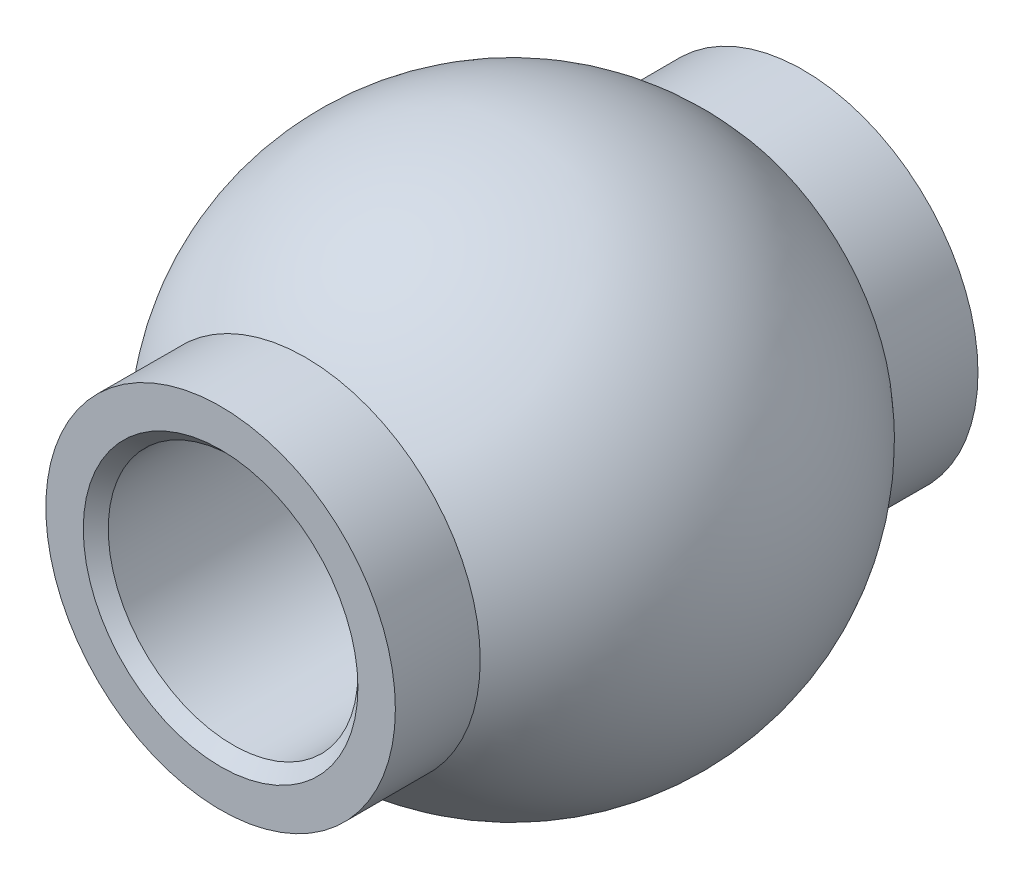
SolidWorks part; units mm, degrees
ref_plane "Front" through (0, 0, 0) normal (0, 0, 1) x (1, 0, 0)
ref_plane "Top" through (0, 0, 0) normal (0, 1, 0) x (1, 0, 0)
ref_plane "Right" through (0, 0, 0) normal (1, 0, 0) x (0, 0, -1)
sketch "Sketch1" plane through (0, 0, 0) normal (0, 0, 1) x (1, 0, 0)
  line L0 (0, 0) -> (0, -34.925)
  line L1 (0, -34.925) -> (4.7625, -34.925)
  line L2 (4.7625, -34.925) -> (4.7625, 0)
  line L3 (4.7625, 0) -> (0, 0)
  line L5 (0, 33.3375) -> (0, 0) construction
  line L6 (0, 33.3375) -> (14.2875, 33.3375) construction
  line L7 (14.2875, 33.3375) -> (14.2875, 19.05) construction
  line L8 (-4.7625, -34.925) -> (-4.7625, 0) construction
  line L9 (3.8092, -34.925) -> (4.7625, -33.9717)
  line L10 (4.8772, -34.8588) -> (4.8772, -35.918) construction
  line L11 (4.8772, -35.918) -> (3.9599, -35.3884) construction
  line L12 (3.9599, -35.3884) -> (4.8772, -34.8588) construction
  line L13 (3.9599, -35.3884) -> (4.0745, -35.3884) construction
  line L14 (4.8772, -35.3884) -> (4.7625, -35.3884) construction
  line L15 (4.0745, -35.4546) -> (4.0745, -35.3222) construction
  line L16 (4.7625, -35.8518) -> (4.7625, -34.925) construction
  line L17 (4.8198, -35.8849) -> (4.8198, -34.8919) construction
  arc A0 (8.5725, 7.62) -> (0, 33.3375) centre (0, 19.05) ccw construction
  circle A1 centre (0, 19.05) radius 4.7625 construction
  circle A2 centre (0, 19.05) radius 10.3187 construction
  circle A3 centre (0, 19.05) radius 10.8347 construction
  arc A4 (4.7625, 0) -> (8.5725, 7.62) centre (14.2875, 0) cw construction
  point P16 (-4.7625, -31.2179)
  point P28 (4.0745, -35.3884)
  point P31 (4.7625, -35.3884)
  point P34 (4.8198, -35.3884)
  dimension "Ball Dia" = 20.6375
  dimension "D1" = 21.6694
  dimension "ID" = 9.525
  dimension "D2" = 3.7071
  dimension "D3" = 45
  dimension "D4" = 0.9533
  dimension "Pitch" = 1.0592
  dimension "D5" = 0.1324
  dimension "Thread Size" = 9.525
  dimension "Overall Width" = 28.575
  dimension "Shank Thread Length" = 34.925
  dimension "Shank Center Length" = 53.975
sketch "Sketch2" plane through (0, 0, 0) normal (1, 0, 0) x (0, 0, -1)
  line L0 (-11.1125, 19.05) -> (11.1125, 19.05)
  line L2 (0, 25.7175) -> (0, 12.3825)
  line L3 (0, 23.8125) -> (0, 14.2875) construction
  line L4 (11.1125, 25.7175) -> (-11.1125, 25.7175)
  line L5 (11.1125, 23.8125) -> (-11.1125, 23.8125)
  line L6 (11.1125, 14.2875) -> (-11.1125, 14.2875)
  line L7 (11.1125, 12.3825) -> (-11.1125, 12.3825)
  line L8 (0, 19.05) -> (-11.1125, 24.8348) construction
  line L9 (0, 19.05) -> (-11.1125, 13.2652) construction
  point P0 (0, 23.8125)
  point P4 (0, 19.05)
  point P9 (0, 19.05)
  point P10 (0, 14.2875)
  point P18 (0, 23.8125)
  point P21 (0, 25.7175)
  point P24 (0, 14.2875)
  point P27 (0, 12.3825)
  dimension "D1" = 13.335
  dimension "Overall Thickness" = 22.225
  dimension "Maximum Ball Swivel" = 55
sketch "Sketch13" plane through (0, 0, 0) normal (0, 0, 1) x (1, 0, 0)
  line L0 (3.8092, -34.925) -> (4.7625, -33.9717) construction
  line L1 (3.8092, -34.925) -> (4.7625, -33.9717)
  line L4 (0, 0) -> (0, -34.925)
  line L5 (0, -34.925) -> (4.7625, -34.925)
  line L6 (4.7625, -34.925) -> (4.7625, 0)
  line L7 (4.7625, 0) -> (0, 0)
  line L8 (0, 0) -> (0, -34.925)
  line L9 (0, -34.925) -> (3.8092, -34.925)
  line L10 (4.7625, -33.9717) -> (4.7625, 0)
  line L11 (4.7625, 0) -> (0, 0)
  dimension "D1" = 0
sketch "Sketch4" plane through (0, 0, 0) normal (0, 0, 1) x (1, 0, 0)
  line L0 (4.7625, 0) -> (0, 0) construction
  line L1 (0, 8.7312) -> (0, 0)
  line L2 (0, 33.3375) -> (0, 0) construction
  line L3 (4.7625, 0) -> (0, 0)
  line L5 (0, 33.3375) -> (0, 29.3687)
  line L6 (0, 33.3375) -> (0, 35.8775) construction
  arc A0 (8.5725, 7.62) -> (0, 33.3375) centre (0, 19.05) ccw construction
  arc A1 (8.5725, 7.62) -> (0, 33.3375) centre (0, 19.05) ccw
  arc A2 (8.5725, 7.62) -> (4.7625, 0) centre (14.2875, 0) ccw construction
  arc A3 (8.5725, 7.62) -> (4.7625, 0) centre (14.2875, 0) ccw
  circle A4 centre (0, 19.05) radius 10.3187 construction
  arc A5 (0, 8.7312) -> (0, 29.3687) centre (0, 19.05) ccw
  dimension "D1" = 2.54
sketch "Sketch7" plane through (0, 0, 0) normal (0, 0, 1) x (1, 0, 0)
  line L0 (0, 29.3687) -> (0, 8.7312)
  line L1 (0, 33.3375) -> (0, 0) construction
  line L2 (0, 0) -> (0, 8.7312) construction
  arc A0 (0, 8.7312) -> (0, 29.3687) centre (0, 19.05) ccw
  circle A1 centre (0, 19.05) radius 10.3187 construction
revolve "Revolve3" add sketch "Sketch7" angle 360 about L2
sketch "Sketch10" plane through (0, 0, 0) normal (0, 0, 1) x (1, 0, 0)
  circle A0 centre (0, 19.05) radius 4.7625 construction
  circle A1 centre (0, 19.05) radius 4.7625
extrude "Cut-Extrude4" cut sketch "Sketch10" against normal through all and the other way through all
sketch "Sketch12" plane through (0, 0, 0) normal (0, 0, 1) x (1, 0, 0)
  circle A0 centre (0, 19.05) radius 6.6675
  circle A1 centre (0, 19.05) radius 4.7625 construction
  circle A2 centre (0, 19.05) radius 4.7625
  dimension "D1" = 13.335
extrude "Extrude1" add sketch "Sketch12" against normal up to vertex (11.1125 mm away) and the other way up to vertex (11.1125 mm away) up to point (0, 19.05, -11.1125) other way up to point (0, 19.05, 11.1125)
chamfer "Chamfer1" distance 0.4762 angle 45 2 edges at (4.7625, 19.05, -11.1125) (4.7625, 19.05, 11.1125)
sketch "Sketch15" plane through (0, 0, 0) normal (0, 0, 1) x (1, 0, 0)
  line L0 (4.0745, -35.3222) -> (4.8198, -34.8919)
  line L1 (4.8198, -34.8919) -> (4.8198, -35.8849)
  line L2 (4.8198, -35.8849) -> (4.0745, -35.4546)
  line L3 (4.0745, -35.4546) -> (4.0745, -35.3222)
sketch "Sketch16" plane through (0, 0, 0) normal (0, 1, 0) x (1, 0, 0)
  circle A0 centre (0, 0) radius 4.7625
equation "\"D1@Sketch1\"=\"Ball Dia@Sketch1\"*1.05"
equation "\"D1@Chamfer1\" = \"ID@Sketch1\" / 20"
equation "\"D1@Sketch12\"= \"ID@Sketch1\" * 1.4"
equation "\"D5@Sketch1\"=\"Pitch@Sketch1\"/8"
equation "\"D4@Sketch1\"=\"Pitch@Sketch1\"*.9"
equation "\"D3\"= \"Shank Thread Length@Sketch1\" + \"Pitch@Sketch1\""
equation "\"D4\"= \"Pitch@Sketch1\""
equation "\"D2@Sketch1\"=\"Pitch@Sketch1\"*3.5"
equation "\"D1@Sketch2\"=\"ID@Sketch1\"*1.4"
